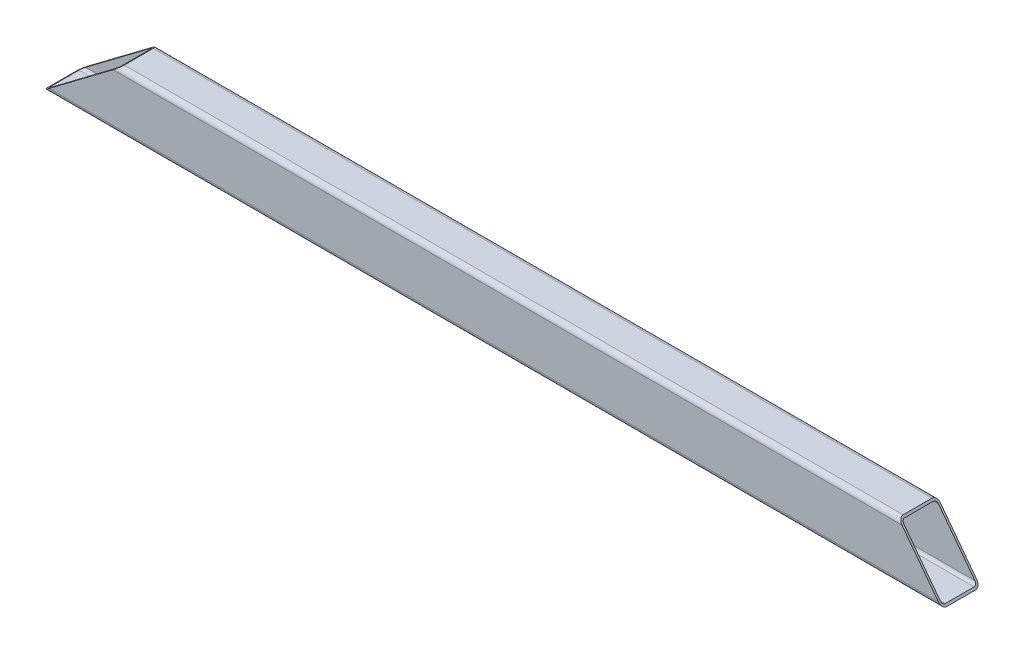
SolidWorks part; units mm, degrees
material "Acier non allié"
ref_plane "Plan de face" through (0, 0, 0) normal (0, 0, 1) x (1, 0, 0)
ref_plane "Plan de dessus" through (0, 0, 0) normal (0, 1, 0) x (1, 0, 0)
ref_plane "Plan de droite" through (0, 0, 0) normal (1, 0, 0) x (0, 0, -1)
sketch "Esquisse1" plane through (0, 0, 0) normal (0, 0, 1) x (1, 0, 0)
  line L0 (-941.8082, 0) -> (941.8082, 0)
  point P2 (0, 0)
  dimension "D1" = 1883.6164
other "Elément mécano-soudé1"
ref_plane "Plan1" through (-941.8082, 0, 0) normal (1, 0, 0) x (0, 1, 0)
sketch "Esquisse15" plane through (-941.8082, 0, 0) normal (1, 0, 0) x (0, 1, 0)
  line L0 (0, 40) -> (0, -40) construction
  line L1 (-50, 40) -> (50, 40)
  line L2 (60, 30) -> (60, -30)
  line L3 (-60, 30) -> (-60, -30)
  line L4 (50, -40) -> (-50, -40)
  line L5 (-60, 0) -> (60, 0) construction
  line L6 (-50, 36) -> (50, 36)
  line L7 (56, 30) -> (56, -30)
  line L8 (50, -36) -> (-50, -36)
  line L9 (-56, 30) -> (-56, -30)
  line L10 (-56, 36) -> (56, 36) construction
  line L11 (-56, 36) -> (-56, -36) construction
  line L12 (56, -36) -> (-56, -36) construction
  line L13 (56, 36) -> (56, -36) construction
  line L14 (-60, 40) -> (-60, -40) construction
  line L15 (-60, 40) -> (60, 40) construction
  line L16 (60, -40) -> (-60, -40) construction
  line L17 (60, 40) -> (60, -40) construction
  arc A0 (-50, 36) -> (-56, 30) centre (-50, 30) ccw
  arc A1 (-50, -36) -> (-56, -30) centre (-50, -30) cw
  arc A2 (56, -30) -> (50, -36) centre (50, -30) cw
  arc A3 (50, 36) -> (56, 30) centre (50, 30) cw
  arc A4 (-60, 30) -> (-50, 40) centre (-50, 30) cw
  arc A5 (-60, -30) -> (-50, -40) centre (-50, -30) ccw
  arc A6 (60, -30) -> (50, -40) centre (50, -30) cw
  arc A7 (50, 40) -> (60, 30) centre (50, 30) cw
  point P28 (-60, 40)
  point P38 (-60, -40)
  point P39 (60, -40)
  point P40 (60, 40)
  point P41 (0, 0)
  dimension "D4" = 6
  dimension "D5" = 10
  dimension "D1" = 120
  dimension "D2" = 80
  dimension "D3" = 4
sketch "Esquisse12" plane through (0, 0, 40) normal (0, 0, 1) x (1, 0, 0)
  line L0 (941.8082, -60) -> (851.3817, 60)
  line L2 (941.8082, 60) -> (-941.8082, 60) construction
  line L3 (851.3817, 60) -> (941.8082, 60)
  line L6 (941.8082, 60) -> (941.8082, -60)
  line L7 (-941.8082, -60) -> (-782.5628, 60)
  line L8 (-782.5628, 60) -> (-941.8082, 60)
  line L9 (-941.8082, 60) -> (-941.8082, -60)
  dimension "D1" = 37
  dimension "D2" = 53
extrude "Extrusion1" cut sketch "Esquisse12" against normal through all
sketch "Esquisse13" plane through (0, 0, 40) normal (0, 0, 1) x (1, 0, 0)
  line L0 (-1042.1753, -60) -> (-925.1918, -60)
  line L1 (941.8082, -60) -> (-941.8082, -60) construction
  line L2 (-925.1918, -60) -> (-765.9464, 60)
  line L4 (-765.9464, 60) -> (-882.9299, 60)
  line L5 (-882.9299, 60) -> (-1042.1753, -60)
  line L6 (851.3817, 60) -> (-782.5628, 60) construction
  line L7 (-928.5378, -50) -> (-795.8333, 50) construction
  dimension "D1" = 10
extrude "Extrusion2" cut sketch "Esquisse13" against normal through all
